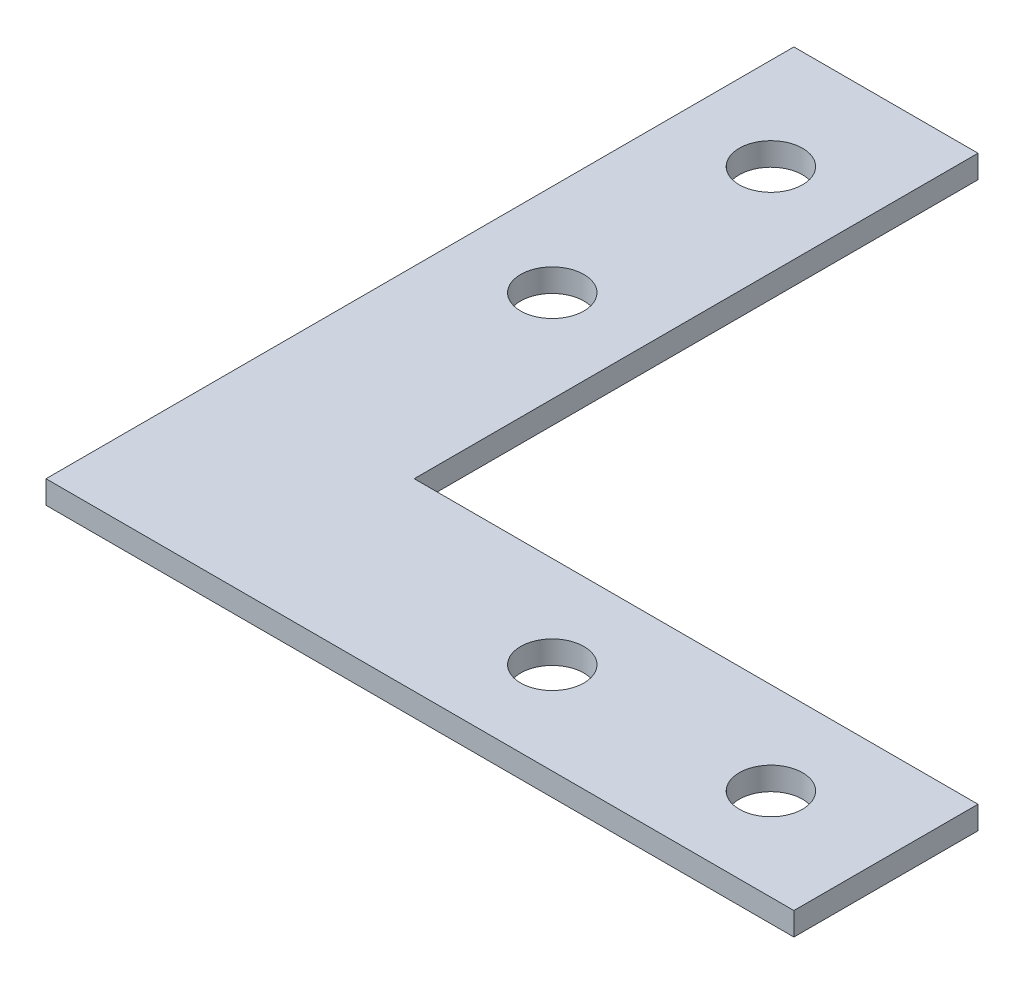
SolidWorks part; units mm, degrees
ref_plane "前视基准面" through (0, 0, 0) normal (0, 0, 1) x (1, 0, 0)
ref_plane "上视基准面" through (0, 0, 0) normal (0, 1, 0) x (1, 0, 0)
ref_plane "右视基准面" through (0, 0, 0) normal (1, 0, 0) x (0, 0, -1)
sketch "草图1" plane through (0, 0, 0) normal (0, 1, 0) x (1, 0, 0)
  line L0 (0, 0) -> (0, 65)
  line L5 (0, 65) -> (16, 65)
  line L6 (16, 65) -> (16, 16)
  line L7 (16, 16) -> (65, 16)
  line L8 (65, 16) -> (65, 0)
  line L9 (65, 0) -> (0, 0)
  line L10 (8, 36) -> (8, 70.7924) construction
  line L11 (0, 8) -> (35.4597, 8) construction
  circle A0 centre (8, 55) radius 2.75
  circle A1 centre (8, 36) radius 2.75
  circle A2 centre (36, 8) radius 2.75
  circle A3 centre (55, 8) radius 2.75
  point P12 (8, 8)
  point P22 (8, 8)
  dimension "D5" = 5.5
  dimension "D6" = 5.5
  dimension "D1" = 16
  dimension "D2" = 16
  dimension "D3" = 65
  dimension "D4" = 65
  dimension "D7" = 19
  dimension "D8" = 10
  dimension "D9" = 8
  dimension "D10" = 8
  dimension "D11" = 2
extrude "凸台-拉伸1" add sketch "草图1" along normal blind 2
